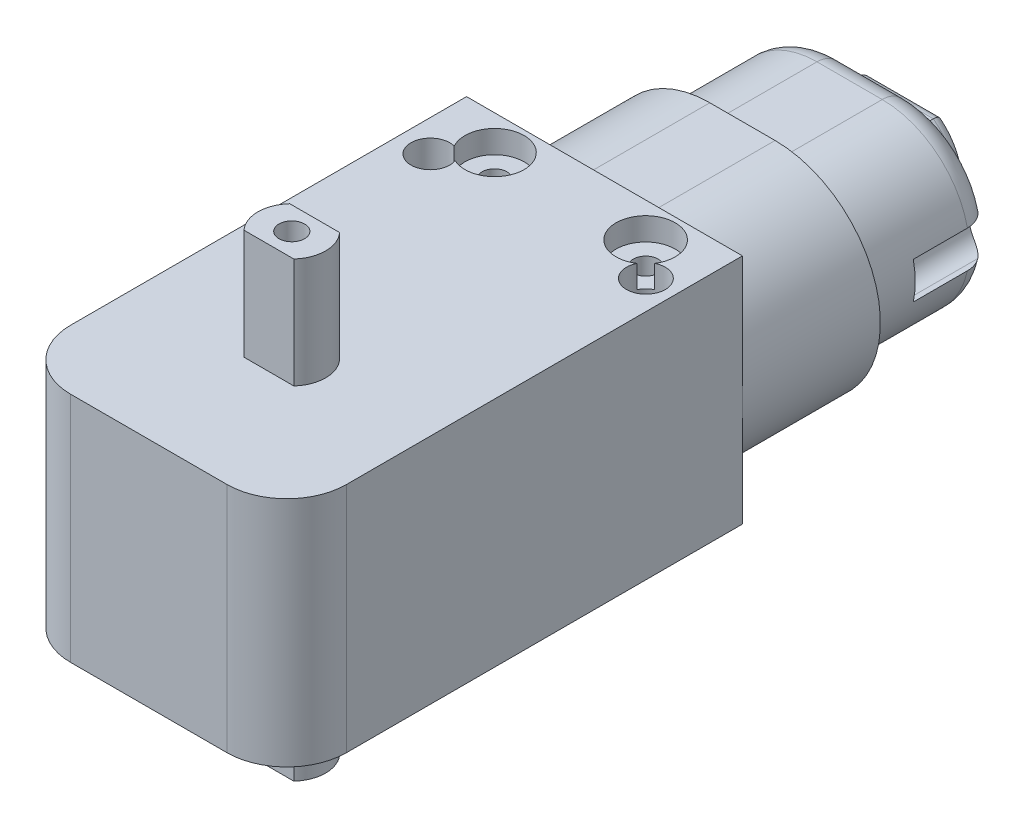
SolidWorks part; units mm, degrees
ref_plane "Front Plane" through (0, 0, 0) normal (0, 0, 1) x (1, 0, 0)
ref_plane "Top Plane" through (0, 0, 0) normal (0, 1, 0) x (1, 0, 0)
ref_plane "Right Plane" through (0, 0, 0) normal (1, 0, 0) x (0, 0, -1)
sketch "Sketch2" plane through (0, 0, 0) normal (1, 0, 0) x (0, 0, -1)
  line L1 (-18.5, 9.43) -> (18.5, 9.43)
  line L2 (-18.5, 9.43) -> (-18.5, -9.43)
  line L3 (-18.5, -9.43) -> (18.5, -9.43)
  line L4 (18.5, 9.43) -> (18.5, -9.43)
  line L5 (-18.5, 9.43) -> (18.5, -9.43) construction
  line L6 (-18.5, -9.43) -> (18.5, 9.43) construction
  point P0 (0, 0)
  dimension "D1" = 37
  dimension "D2" = 18.86
extrude "Boss-Extrude1" add sketch "Sketch2" along normal mid plane 22.4
fillet "Fillet1" radius 4.85 2 edges at (-11.2, 0, 18.5) (11.2, 0, 18.5)
sketch "Sketch3" plane through (0, 0, -18.5) normal (0, 0, -1) x (-1, 0, 0)
  line L0 (-2.65, -0.88) -> (2.65, -0.88) construction
  line L1 (-2.65, 7.67) -> (2.65, 7.67)
  line L2 (-2.65, -9.43) -> (2.65, -9.43)
  line L3 (-11.2, -9.43) -> (-11.2, 9.43) construction
  line L4 (11.2, -9.43) -> (11.2, 9.43) construction
  line L5 (-11.2, -9.43) -> (11.2, -9.43) construction
  arc A0 (-2.65, 7.67) -> (-2.65, -9.43) centre (-2.65, -0.88) ccw
  arc A1 (2.65, -9.43) -> (2.65, 7.67) centre (2.65, -0.88) ccw
  point P3 (0, -0.88)
  dimension "D3" = 17.1
extrude "Boss-Extrude2" add sketch "Sketch3" along normal blind 11.2
sketch "Sketch4" plane through (0, 0, -29.7) normal (0, 0, -1) x (-1, 0, 0)
  line L4 (-2.65, -7.96) -> (2.65, -7.96)
  line L5 (2.65, 6.2) -> (-2.65, 6.2)
  line L6 (-2.65, -7.96) -> (2.65, -7.96)
  line L7 (2.65, 6.2) -> (-2.65, 6.2)
  arc A4 (-2.65, 6.2) -> (-2.65, -7.96) centre (-2.65, -0.88) ccw
  arc A5 (2.65, -7.96) -> (2.65, 6.2) centre (2.65, -0.88) ccw
  arc A6 (-2.65, 6.2) -> (-2.65, -7.96) centre (-2.65, -0.88) ccw
  arc A7 (2.65, -7.96) -> (2.65, 6.2) centre (2.65, -0.88) ccw
  dimension "D1" = 1.47
extrude "Boss-Extrude3" add sketch "Sketch4" along normal blind 13.3
sketch "Sketch5" plane through (0, 0, -43) normal (0, 0, -1) x (-1, 0, 0)
  line L0 (-9.73, -0.88) -> (9.73, -0.88) construction
  line L1 (-3, 3.12) -> (3, 3.12)
  line L4 (-2.65, -7.96) -> (2.65, -7.96)
  line L5 (2.65, 6.2) -> (-2.65, 6.2)
  line L6 (-2.65, -7.96) -> (2.65, -7.96)
  line L7 (2.65, 6.2) -> (-2.65, 6.2)
  arc A0 (-3, 3.12) -> (3, 3.12) centre (0, -0.88) ccw
  arc A1 (-2.65, 6.2) -> (-2.65, -7.96) centre (-2.65, -0.88) ccw construction
  arc A2 (2.65, -7.96) -> (2.65, 6.2) centre (2.65, -0.88) ccw construction
  arc A5 (-2.65, 6.2) -> (-2.65, -7.96) centre (-2.65, -0.88) ccw
  arc A6 (2.65, -7.96) -> (2.65, 6.2) centre (2.65, -0.88) ccw
  arc A7 (-2.65, 6.2) -> (-2.65, -7.96) centre (-2.65, -0.88) ccw
  arc A8 (2.65, -7.96) -> (2.65, 6.2) centre (2.65, -0.88) ccw
  dimension "D1" = 10
  dimension "D3" = 9.73
  dimension "D2" = 6
  dimension "D4" = 0
extrude "Cut-Extrude1" cut sketch "Sketch5" against normal blind 2.5
fillet "Fillet2" radius 0.8 2 edges at (0, -5.88, -43) (0, 3.12, -43)
fillet "Fillet3" radius 2.1 4 edges at (0, -7.96, -40.5) (9.73, -0.88, -40.5) (0, 6.2, -40.5) (-9.73, -0.88, -40.5)
sketch "Sketch6" plane through (0, 0, -40.5) normal (0, 0, -1) x (-1, 0, 0)
  line L0 (-11.2, -0.88) -> (11.2, -0.88) construction
  line L1 (9.13, -0.88) -> (11.2, -0.88) construction
  line L2 (9.13, 0.62) -> (11.2, 0.62)
  line L3 (9.13, -2.38) -> (11.2, -2.38)
  line L4 (0, -0.88) -> (0, -4.4243) construction
  arc A0 (-2.65, 7.67) -> (-2.65, -9.43) centre (-2.65, -0.88) ccw construction
  arc A2 (9.13, 0.62) -> (9.13, -2.38) centre (9.13, -0.88) ccw
  arc A3 (11.2, -2.38) -> (11.2, 0.62) centre (11.2, -0.88) ccw
  arc A4 (2.65, -5.86) -> (2.65, 4.1) centre (2.65, -0.88) ccw construction
  point P9 (10.165, -0.88)
  dimension "D1" = 3
extrude "Cut-Extrude2" cut sketch "Sketch6" against normal blind 6.5
mirror "Mirror1" about plane through (0, 0, 0) normal (1, 0, 0) of "Cut-Extrude2"
sketch "Sketch10" plane through (0, 9.43, 0) normal (0, 1, 0) x (1, 0, 0)
  line L0 (-1.9156, -8.86) -> (2.1356, -8.86)
  line L1 (-1.9156, -5.14) -> (2.1356, -5.14)
  line L2 (-1.9156, -8.86) -> (2.1356, -5.14) construction
  line L3 (2.1356, -8.86) -> (-1.9156, -5.14) construction
  line L9 (-11.2, 18.5) -> (-11.2, -13.65) construction
  line L10 (6.35, -18.5) -> (-6.35, -18.5) construction
  arc A0 (-1.9156, -5.14) -> (-1.9156, -8.86) centre (0.11, -7) ccw
  arc A1 (2.1356, -8.86) -> (2.1356, -5.14) centre (0.11, -7) ccw
  dimension "D1" = 5.5
  dimension "D4" = 9.64
  dimension "D3" = 11.31
  dimension "D2" = 3.72
extrude "Boss-Extrude5" add sketch "Sketch10" along normal blind 8.93
sketch "Sketch11" plane through (0, 18.36, 0) normal (0, 1, 0) x (1, 0, 0)
  circle A0 centre (0.11, -7) radius 1.04
  arc A1 (-1.9156, -5.14) -> (-1.9156, -8.86) centre (0.11, -7) ccw construction
  dimension "D1" = 2.08
extrude "Cut-Extrude4" cut sketch "Sketch11" against normal blind 8.93
mirror "Mirror3" about plane through (0, 0, 0) normal (0, 1, 0) of "Cut-Extrude4", "Boss-Extrude5"
sketch "Sketch12" plane through (0, -9.43, 0) normal (0, -1, 0) x (1, 0, 0)
  line L0 (11.2, -18.5) -> (2.65, -18.5) construction
  line L1 (-11.2, 13.65) -> (-11.2, -18.5) construction
  circle A0 centre (8.8614, -13) radius 1.575
  circle A1 centre (-8.6386, -13) radius 1.575
  dimension "D1" = 3.15
  dimension "D2" = 3.15
  dimension "D4" = 5.5
  dimension "D5" = 2.5614
  dimension "D3" = 17.5
extrude "Cut-Extrude5" cut sketch "Sketch12" against normal up to body separate body
sketch "Sketch13" plane through (0, 9.43, 0) normal (0, 1, 0) x (1, 0, 0)
  line L0 (6.14, 15.7) -> (-6.13, 15.7) construction
  line L1 (-2.65, 18.5) -> (-11.2, 18.5) construction
  line L2 (-11.2, 18.5) -> (-11.2, -13.65) construction
  circle A0 centre (6.14, 15.7) radius 2.4
  circle A1 centre (-6.13, 15.7) radius 2.4
  dimension "D2" = 4.8
  dimension "D3" = 4.8
  dimension "D4" = 2.8
  dimension "D5" = 5.07
  dimension "D1" = 12.27
extrude "Cut-Extrude6" cut sketch "Sketch13" against normal blind 1.85
sketch "Sketch14" plane through (0, 7.58, 0) normal (0, 1, 0) x (1, 0, 0)
  circle A0 centre (-6.13, 15.7) radius 1
  circle A1 centre (6.14, 15.7) radius 1
  dimension "D1" = 2
  dimension "D2" = 2
extrude "Cut-Extrude7" cut sketch "Sketch14" against normal blind 10
